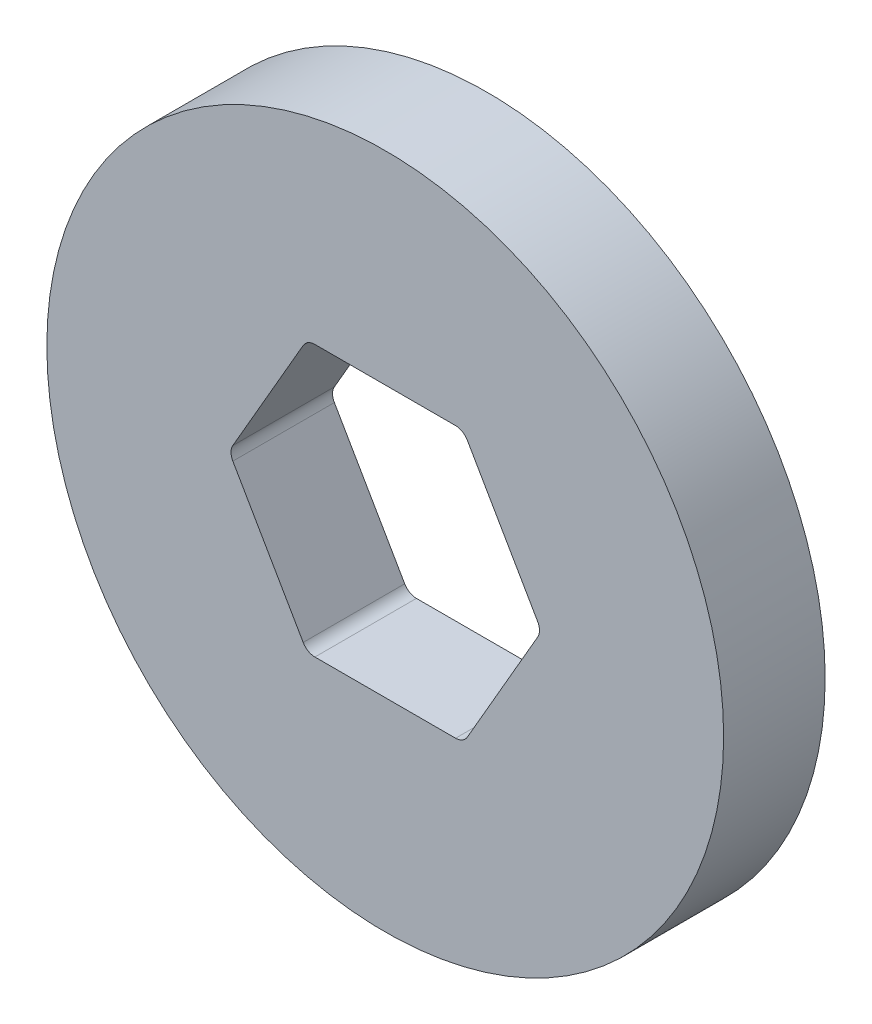
SolidWorks part; units mm, degrees
ref_plane "Front Plane" through (0, 0, 0) normal (0, 0, 1) x (1, 0, 0)
ref_plane "Top Plane" through (0, 0, 0) normal (0, 1, 0) x (1, 0, 0)
ref_plane "Right Plane" through (0, 0, 0) normal (1, 0, 0) x (0, 0, -1)
sketch "Sketch1" plane through (0, 0, 0) normal (0, 0, 1) x (1, 0, 0)
  line L1 (23.094, 0) -> (11.547, 20)
  line L2 (11.547, 20) -> (-11.547, 20)
  line L3 (-11.547, 20) -> (-23.094, 0)
  line L4 (-23.094, 0) -> (-11.547, -20)
  line L5 (-11.547, -20) -> (11.547, -20)
  line L6 (11.547, -20) -> (23.094, 0)
  circle A0 centre (0, 0) radius 50
  circle A1 centre (0, 0) radius 20 construction
  dimension "D1" = 100
  dimension "D2" = 40
extrude "Boss-Extrude2" add sketch "Sketch1" along normal blind 15
fillet "Fillet1" radius 2 6 edges at (-11.547, -20, 7.5) (11.547, -20, 7.5) (23.094, 0, 7.5) (11.547, 20, 7.5) (-23.094, 0, 7.5) (-11.547, 20, 7.5)
